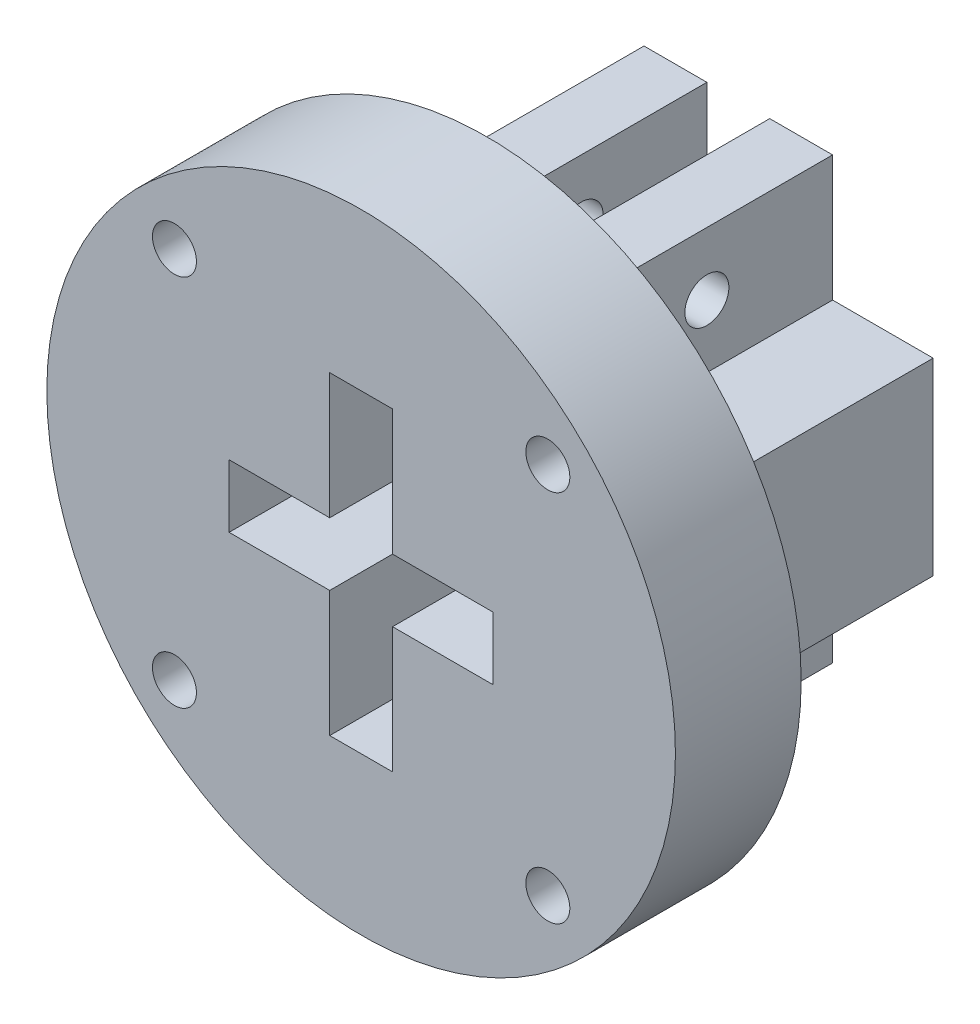
SolidWorks part; units mm, degrees
ref_plane "前视基准面" through (0, 0, 0) normal (0, 0, 1) x (1, 0, 0)
ref_plane "上视基准面" through (0, 0, 0) normal (0, 1, 0) x (1, 0, 0)
ref_plane "右视基准面" through (0, 0, 0) normal (1, 0, 0) x (0, 0, -1)
sketch "草图1" plane through (0, 0, 0) normal (0, 0, 1) x (1, 0, 0)
  line L0 (-10.5, 2.5) -> (-2.5, 2.5)
  line L1 (10.5, -2.5) -> (-10.5, -2.5) construction
  line L2 (10.5, -2.5) -> (10.5, 2.5) construction
  line L3 (10.5, 2.5) -> (-10.5, 2.5) construction
  line L4 (-10.5, -2.5) -> (-10.5, 2.5) construction
  line L5 (0, 2.5) -> (0, -2.5) construction
  line L6 (10.5, 0) -> (-10.5, 0) construction
  line L7 (-2.5, -12.5) -> (2.5, -12.5) construction
  line L8 (-2.5, -12.5) -> (-2.5, 12.5) construction
  line L9 (-2.5, 12.5) -> (2.5, 12.5) construction
  line L10 (2.5, -12.5) -> (2.5, 12.5) construction
  line L11 (0, 12.5) -> (0, -12.5) construction
  line L12 (-2.5, 0) -> (2.5, 0) construction
  line L13 (-2.5, 2.5) -> (-2.5, 12.5)
  line L14 (-2.5, 12.5) -> (2.5, 12.5)
  line L15 (2.5, 12.5) -> (2.5, 2.5)
  line L16 (2.5, 2.5) -> (10.5, 2.5)
  line L17 (10.5, 2.5) -> (10.5, -2.5)
  line L18 (10.5, -2.5) -> (2.5, -2.5)
  line L19 (2.5, -2.5) -> (2.5, -12.5)
  line L20 (2.5, -12.5) -> (-2.5, -12.5)
  line L21 (-2.5, -12.5) -> (-2.5, -2.5)
  line L22 (-2.5, -2.5) -> (-10.5, -2.5)
  line L23 (-10.5, 2.5) -> (-10.5, -2.5)
  line L25 (-15.5, 7.5) -> (-15.5, -7.5)
  line L26 (-15.5, 7.5) -> (-7.5, 7.5)
  line L27 (-7.5, 7.5) -> (-7.5, 17.5)
  line L28 (-7.5, 17.5) -> (7.5, 17.5)
  line L29 (7.5, 17.5) -> (7.5, 7.5)
  line L30 (7.5, 7.5) -> (15.5, 7.5)
  line L31 (15.5, 7.5) -> (15.5, -7.5)
  line L32 (15.5, -7.5) -> (7.5, -7.5)
  line L33 (7.5, -7.5) -> (7.5, -17.5)
  line L34 (7.5, -17.5) -> (-7.5, -17.5)
  line L35 (-7.5, -17.5) -> (-7.5, -7.5)
  line L36 (-7.5, -7.5) -> (-15.5, -7.5)
  point P0 (0, 0)
  point P5 (0, 0)
  dimension "D1" = 5
  dimension "D2" = 5
  dimension "D3" = 10
  dimension "D4" = 8
  dimension "D5" = 5
extrude "凸台-拉伸1" add sketch "草图1" along normal blind 20
sketch "草图2" plane through (0, 0, 20) normal (0, 0, 1) x (1, 0, 0)
  line L0 (-10.5, -2.5) -> (-2.5, -2.5) construction
  line L1 (-2.5, -2.5) -> (-2.5, -12.5) construction
  line L2 (-2.5, -12.5) -> (2.5, -12.5) construction
  line L3 (2.5, -12.5) -> (2.5, -2.5) construction
  line L4 (2.5, -2.5) -> (10.5, -2.5) construction
  line L5 (10.5, -2.5) -> (10.5, 2.5) construction
  line L6 (10.5, 2.5) -> (2.5, 2.5) construction
  line L7 (2.5, 2.5) -> (2.5, 12.5) construction
  line L8 (2.5, 12.5) -> (-2.5, 12.5) construction
  line L9 (-2.5, 12.5) -> (-2.5, 2.5) construction
  line L10 (-2.5, 2.5) -> (-10.5, 2.5) construction
  line L11 (-10.5, -2.5) -> (-2.5, -2.5)
  line L12 (-2.5, -2.5) -> (-2.5, -12.5)
  line L13 (-2.5, -12.5) -> (2.5, -12.5)
  line L14 (2.5, -12.5) -> (2.5, -2.5)
  line L15 (2.5, -2.5) -> (10.5, -2.5)
  line L16 (10.5, -2.5) -> (10.5, 2.5)
  line L17 (10.5, 2.5) -> (2.5, 2.5)
  line L18 (2.5, 2.5) -> (2.5, 12.5)
  line L19 (2.5, 12.5) -> (-2.5, 12.5)
  line L20 (-2.5, 12.5) -> (-2.5, 2.5)
  line L21 (-2.5, 2.5) -> (-10.5, 2.5)
  line L22 (-10.5, 2.5) -> (-10.5, -2.5)
  circle A0 centre (0, 0) radius 25
  dimension "D1" = 50
extrude "凸台-拉伸2" add sketch "草图2" along normal blind 10
sketch "草图5" plane through (0, 0, 0) normal (0, 0, -1) x (-1, 0, 0)
  line L0 (-2.5, 12.5) -> (-2.5, 17.5)
  line L1 (-7.5, 17.5) -> (7.5, 17.5) construction
  line L2 (-2.5, 17.5) -> (2.5, 17.5)
  line L3 (2.5, 17.5) -> (2.5, 12.5)
  line L4 (2.5, 12.5) -> (-2.5, 12.5)
  line L5 (-2.5, -12.5) -> (-2.5, -17.5)
  line L6 (7.5, -17.5) -> (-7.5, -17.5) construction
  line L7 (-2.5, -17.5) -> (2.5, -17.5)
  line L8 (2.5, -17.5) -> (2.5, -12.5)
  line L9 (2.5, -12.5) -> (-2.5, -12.5)
extrude "切除-拉伸2" cut sketch "草图5" against normal up to surface (20 mm away) up to face at (25, 0, 20)
sketch "草图6" plane through (0, 0, 20) normal (0, 0, -1) x (-1, 0, 0)
  line L0 (0, 0) -> (14.8492, 14.8492) construction
  circle A0 centre (0, 0) radius 21 construction
  circle A1 centre (14.8492, 14.8492) radius 1.75
  circle A2 centre (14.8492, -14.8492) radius 1.75
  circle A3 centre (-14.8492, -14.8492) radius 1.75
  circle A4 centre (-14.8492, 14.8492) radius 1.75
  point P14 (0, 0)
  dimension "D1" = 42
  dimension "D2" = 3.5
  dimension "D3" = 4
extrude "切除-拉伸3" cut sketch "草图6" against normal blind 10
sketch "草图7" plane through (-7.5, 0, 0) normal (-1, 0, 0) x (0, 0, 1)
  line L0 (0, 0) -> (20, 0) construction
  line L1 (20, 7.5) -> (20, -7.5) construction
  circle A0 centre (10, 12.5) radius 1.75
  circle A1 centre (10, -12.5) radius 1.75
  dimension "D1" = 3.5
extrude "切除-拉伸4" cut sketch "草图7" against normal blind 38
